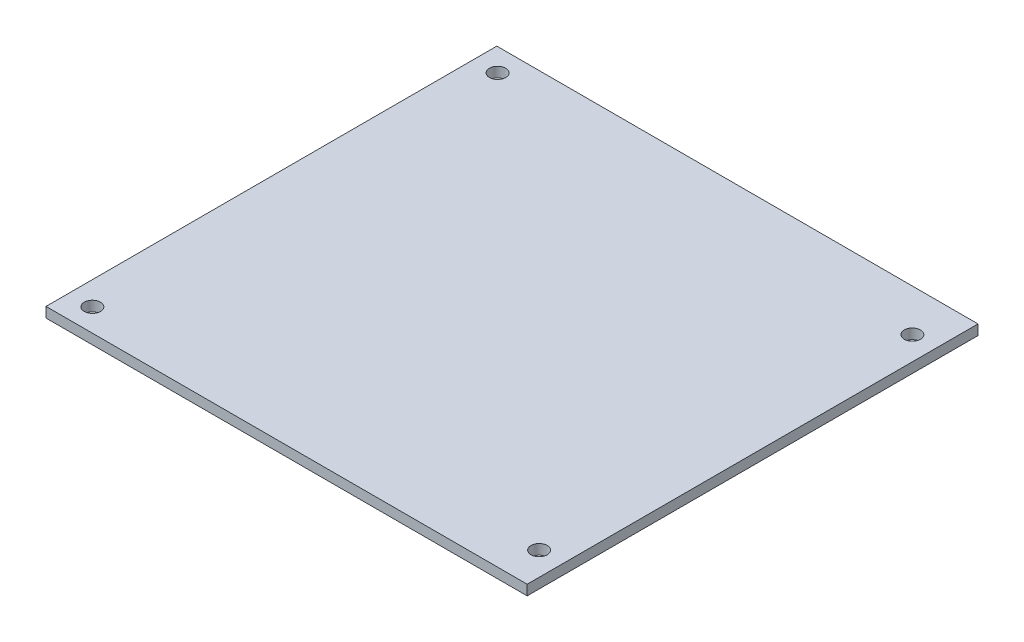
SolidWorks part; units mm, degrees
ref_plane "Front Plane" through (0, 0, 0) normal (0, 0, 1) x (1, 0, 0)
ref_plane "Top Plane" through (0, 0, 0) normal (0, 1, 0) x (1, 0, 0)
ref_plane "Right Plane" through (0, 0, 0) normal (1, 0, 0) x (0, 0, -1)
sketch "Sketch1" plane through (0, 0, 0) normal (0, 1, 0) x (1, 0, 0)
  line L1 (-47.5, -44.505) -> (47.5, -44.505)
  line L2 (-47.5, -44.505) -> (-47.5, 44.505)
  line L3 (-47.5, 44.505) -> (47.5, 44.505)
  line L4 (47.5, -44.505) -> (47.5, 44.505)
  line L5 (-47.5, -44.505) -> (47.5, 44.505) construction
  line L6 (-47.5, 44.505) -> (47.5, -44.505) construction
  circle A0 centre (-42.85, 40) radius 1.6
  circle A1 centre (42.85, 36.2) radius 1.6
  circle A2 centre (-42.85, -40) radius 1.6
  circle A3 centre (42.85, -37.5) radius 1.6
  point P0 (47.5, 44.505)
  point P1 (0, 0)
  point P7 (42.85, 36.2)
  point P8 (42.85, -37.5)
  point P9 (-42.85, 40)
  point P10 (-42.85, -40)
extrude "Boss-Extrude1" add sketch "Sketch1" along normal blind 2
